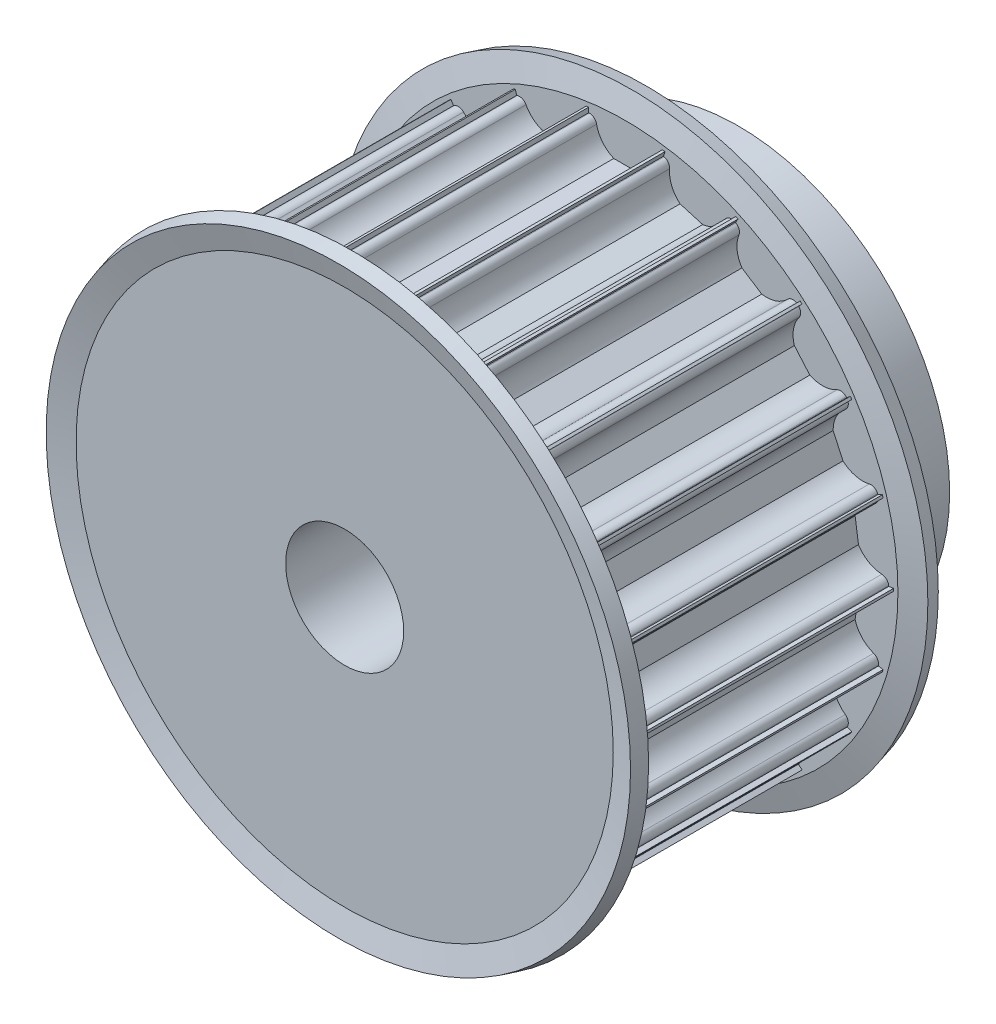
SolidWorks part; units mm, degrees
ref_plane "Front Plane" through (0, 0, 0) normal (0, 0, 1) x (1, 0, 0)
ref_plane "Top Plane" through (0, 0, 0) normal (0, 1, 0) x (1, 0, 0)
ref_plane "Right Plane" through (0, 0, 0) normal (1, 0, 0) x (0, 0, -1)
sketch "Sketch1" plane through (0, 0, 0) normal (1, 0, 0) x (0, 0, -1)
  line L0 (-59.4, 0) -> (75.2, 0) construction
  line L1 (0, 6) -> (0, 27.25)
  line L2 (0, 27.25) -> (30, 27.25)
  line L3 (30, 27.25) -> (30, 21.5)
  line L4 (30, 21.5) -> (40, 21.5)
  line L5 (40, 21.5) -> (40, 6)
  line L6 (40, 6) -> (0, 6)
  dimension "D1" = 30
  dimension "D2" = 15.5
  dimension "D3" = 10
  dimension "D4" = 21.25
  dimension "D5" = 6
revolve "Revolve1" add sketch "Sketch1" angle 360 about L0
sketch "Sketch2" plane through (0, 0, 0) normal (0, 0, 1) x (1, 0, 0)
  line L0 (1.199, 23.75) -> (-1.199, 23.75)
  line L1 (-3.75, 28.5) -> (3.75, 28.5)
  line L2 (-3.75, 28.5) -> (-3.75, 26.5)
  line L3 (-3.75, 26.5) -> (-3.6742, 26.5)
  line L4 (3.75, 28.5) -> (3.75, 26.5)
  line L5 (3.6742, 26.5) -> (3.75, 26.5)
  arc A0 (-2.9394, 25.9) -> (-1.199, 23.75) centre (0, 26.5) ccw
  arc A1 (1.199, 23.75) -> (2.9394, 25.9) centre (0, 26.5) ccw
  arc A2 (-2.9394, 25.9) -> (-3.6742, 26.5) centre (-3.6742, 25.75) ccw
  arc A3 (2.9394, 25.9) -> (3.6742, 26.5) centre (3.6742, 25.75) cw
  point P12 (-3, 26.5)
  point P15 (3, 26.5)
  dimension "D2" = 3
  dimension "D6" = 0.75
  dimension "D1" = 26.5
  dimension "D3" = 7.5
  dimension "D4" = 2
  dimension "D5" = 2.75
extrude "Cut-Extrude1" cut sketch "Sketch2" against normal through all
pattern_circular "CirPattern1" count 22 over 360 about axis through (0, 0, 0) along (0, 0, 1) of "Cut-Extrude1"
sketch "Sketch3" plane through (0, 0, 0) normal (1, 0, 0) x (0, 0, -1)
  line L0 (0, 25.679) -> (0, 23.1257) construction
  line L1 (0, 22.6907) -> (1.4489, 22.6907)
  line L2 (0, 22.6907) -> (0, 27.6907)
  line L3 (0, 27.6907) -> (1.4489, 27.6907) construction
  line L4 (1.4489, 22.6907) -> (1.4489, 27.6907)
  line L5 (1.4489, 27.6907) -> (0, 27.3025)
  line L6 (1.4489, 27.6907) -> (0.8058, 30.0907)
  line L7 (0, 27.3025) -> (-0.6431, 29.7025)
  line L8 (0.8058, 30.0907) -> (-0.6431, 29.7025)
  line L9 (30, 26.9907) -> (0, 26.9907) construction
  line L10 (-17.2062, 0) -> (48.5864, 0) construction
  line L11 (15, 37.7088) -> (15, -11.9445) construction
  line L12 (30, 22.6907) -> (28.5511, 22.6907)
  line L13 (30, 22.6907) -> (30, 27.6907)
  line L14 (28.5511, 22.6907) -> (28.5511, 27.6907)
  line L15 (28.5511, 27.6907) -> (29.1942, 30.0907)
  line L16 (29.1942, 30.0907) -> (30.6431, 29.7025)
  line L17 (30, 27.3025) -> (30.6431, 29.7025)
  dimension "D1" = 5
  dimension "D2" = 0.7
  dimension "D3" = 165
  dimension "D4" = 1.5
  dimension "D5" = 2.4
revolve "Revolve2" add sketch "Sketch3" angle 360 about L10
